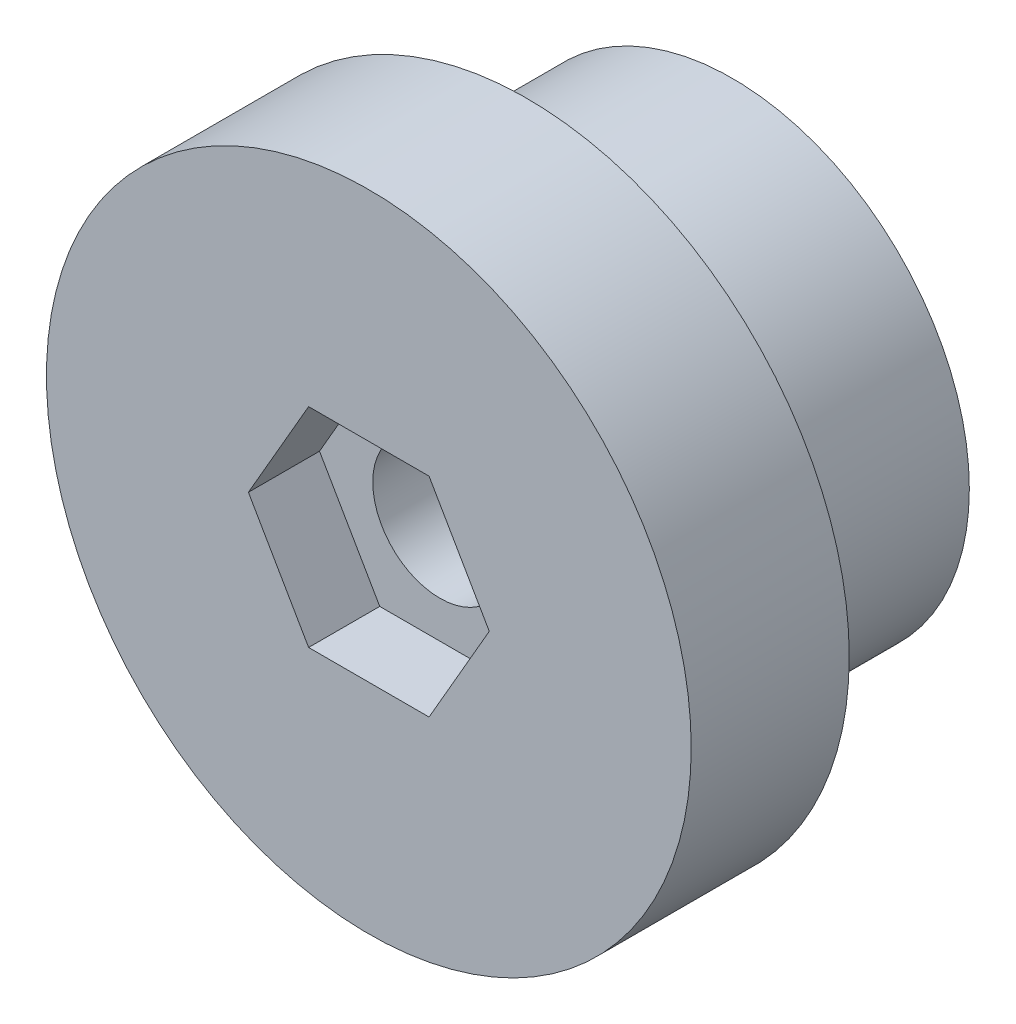
SolidWorks part; units mm, degrees
ref_plane "Plano frontal" through (0, 0, 0) normal (0, 0, 1) x (1, 0, 0)
ref_plane "Plano superior" through (0, 0, 0) normal (0, 1, 0) x (1, 0, 0)
ref_plane "Plano direito" through (0, 0, 0) normal (1, 0, 0) x (0, 0, -1)
sketch "Esboço1" plane through (0, 0, 0) normal (0, 0, 1) x (1, 0, 0)
  circle A0 centre (0, 0) radius 20.4
  circle A1 centre (0, 0) radius 4.25
extrude "Ressalto-extrusão1" add sketch "Esboço1" along normal blind 10
sketch "Esboço2" plane through (0, 0, 10) normal (0, 0, 1) x (1, 0, 0)
  line L1 (3.8105, -6.6) -> (7.621, 0)
  line L2 (7.621, 0) -> (3.8105, 6.6)
  line L3 (3.8105, 6.6) -> (-3.8105, 6.6)
  line L4 (-3.8105, 6.6) -> (-7.621, 0)
  line L5 (-7.621, 0) -> (-3.8105, -6.6)
  line L6 (-3.8105, -6.6) -> (3.8105, -6.6)
  circle A0 centre (0, 0) radius 6.6 construction
extrude "Corte-extrusão1" cut sketch "Esboço2" against normal blind 4.5
sketch "Esboço3" plane through (0, 0, 0) normal (0, 0, 1) x (1, 0, 0)
  line L3 (9.4574, -17.8955) -> (10.1942, -17.4867)
  line L4 (4.4212, 19.7527) -> (5.2392, 19.5516)
  line L5 (-19.3671, 5.8856) -> (-19.1052, 6.6852)
  line L9 (3.9282, 1.749) -> (4.206, 0.894)
  line L10 (-2.15, -3.7239) -> (-2.8773, -3.1955)
  line L11 (-2.8773, 3.1955) -> (-2.15, 3.7239)
  line L15 (10.9302, 12.5566) -> (10.2507, 13.1177)
  line L16 (9.8097, -13.4505) -> (10.5072, -12.9135)
  line L17 (-15.296, -6.5707) -> (-14.9273, -7.3708)
  line L18 (-3.8639, 16.1935) -> (-6.685, 19.1054)
  line L19 (-6.685, 19.1054) -> (-7.4736, 18.8108)
  line L20 (-7.4736, 18.8108) -> (-7.6955, 14.7627)
  line L24 (2.6872, 10.9848) -> (3.7911, 10.6545)
  line L25 (-9.6163, 5.9497) -> (-8.9612, 6.8973)
  line L26 (4.2829, -10.4654) -> (3.1945, -10.8467)
  line L30 (7.6577, -13.0272) -> (8.0565, -12.7847)
  line L31 (7.0438, 13.3688) -> (7.4524, 13.145)
  line L32 (-14.0313, 5.6073) -> (-13.8517, 6.0373)
  line L37 (1.4618, 15.0405) -> (1.8777, 14.3786)
  line L38 (2.7434, 11.216) -> (2.6872, 10.9848)
  line L39 (-0.8827, 11.6772) -> (-0.8695, 11.2744)
  line L40 (0.4364, 14.4944) -> (0.9527, 15.0811)
  circle A0 centre (0.0002, 0.0001) radius 20.2412
  circle A1 centre (0, 0) radius 4.2764
  circle A2 centre (0.0001, 0.0001) radius 16.6477
  circle A3 centre (0.0004, 0.0006) radius 11.2934
  circle A4 centre (0.2794, 0.006) radius 14.9695
sketch "Esboço5" plane through (0, 0, 0) normal (0, 0, -1) x (-1, 0, 0)
  circle A0 centre (0, 0) radius 4.25
  circle A1 centre (0, 0) radius 15
extrude "Ressalto-extrusão2" add sketch "Esboço5" along normal blind 13
